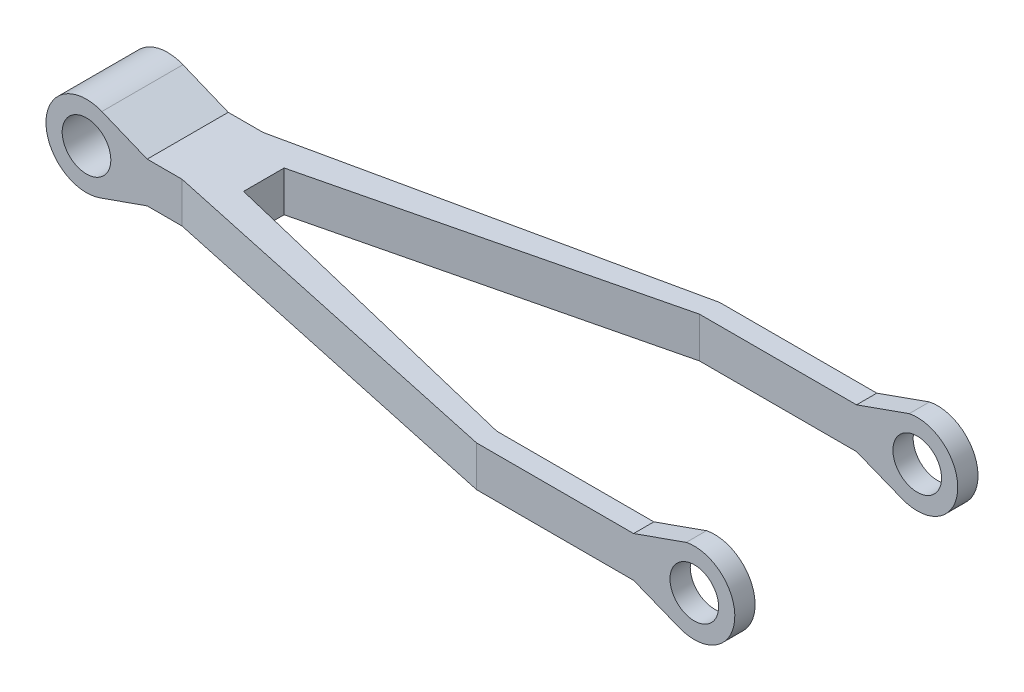
SolidWorks part; units mm, degrees
ref_plane "Front Plane" through (0, 0, 0) normal (0, 0, 1) x (1, 0, 0)
ref_plane "Top Plane" through (0, 0, 0) normal (0, 1, 0) x (1, 0, 0)
ref_plane "Right Plane" through (0, 0, 0) normal (1, 0, 0) x (0, 0, -1)
sketch "Sketch1" plane through (0, 0, 0) normal (0, 0, 1) x (1, 0, 0)
  line L0 (-349.8733, 24.6435) -> (-405.7801, 47.538)
  line L1 (350.1267, -25.3565) -> (-349.8733, -25.3565)
  line L3 (350.1267, 24.6435) -> (-349.8733, 24.6435)
  line L7 (-349.8733, -25.3565) -> (-408.1023, -45.8872)
  line L9 (0.1267, 24.6435) -> (350.1267, 24.6435) construction
  line L10 (350.1267, 24.6435) -> (415.1579, 47.7515)
  line L11 (350.1267, -25.3565) -> (406.5613, -47.7462)
  line L14 (-349.8733, 24.6435) -> (0.1267, 24.6435) construction
  arc A0 (-405.7801, 47.538) -> (-408.1023, -45.8872) centre (-424.7285, 1.2675) ccw
  arc A1 (406.5613, -47.7462) -> (401.7026, 42.9703) centre (425, -1.2703) ccw
  point P0 (0, 0)
  dimension "D4" = 100
  dimension "D5" = 100
  dimension "D1" = 700
  dimension "D2" = 50
extrude "Boss-Extrude1" add sketch "Sketch1" along normal blind 300 contours L11 A1 L10 L3 L0 A0 L7 L1
sketch "Sketch3" plane through (0, 24.6435, 0) normal (0, 1, 0) x (1, 0, 0)
  line L0 (156.3847, -275) -> (-255.9514, -175)
  line L1 (350.1267, -300) -> (-349.8733, -300) construction
  line L2 (-306.817, 0) -> (-306.817, -300) construction
  line L3 (350.1267, 0) -> (-349.8733, 0) construction
  line L4 (-306.817, -150) -> (-102.2723, -150) construction
  line L5 (-255.9514, -175) -> (-255.9514, -150)
  line L6 (-255.9514, -150) -> (-255.9514, -125)
  line L7 (-255.9514, -125) -> (156.3847, -25)
  line L8 (156.3847, -25) -> (156.3847, -150) construction
  line L9 (156.3847, -150) -> (156.3847, -275) construction
  line L10 (156.3847, -275) -> (523.2664, -275)
  line L11 (156.3847, -25) -> (646.791, -25)
  line L12 (156.3847, 0) -> (-306.817, -100)
  line L13 (156.3847, -300) -> (-306.817, -200)
  line L14 (156.3847, -300) -> (568.0939, -300)
  line L15 (568.0939, -300) -> (523.2664, -275)
  line L16 (156.3847, 0) -> (660.0038, 0)
  line L17 (660.0038, 0) -> (646.791, -25)
  line L18 (-306.817, -100) -> (-623.6055, -100)
  line L19 (-623.6055, -100) -> (-623.6055, -200)
  line L20 (-623.6055, -200) -> (-306.817, -200)
  dimension "D1" = 25
  dimension "D2" = 25
  dimension "D3" = 50
  dimension "D4" = 50
extrude "Cut-Extrude1" cut sketch "Sketch3" against normal blind 300 flip side to cut
sketch "Sketch5" plane through (0, 24.6435, 0) normal (0, 1, 0) x (1, 0, 0)
  line L0 (156.3847, -25) -> (555.9211, -25)
  line L1 (555.9211, -25) -> (555.9211, -275)
  line L2 (555.9211, -275) -> (156.3847, -275)
  line L3 (156.3847, -275) -> (-255.9514, -175) construction
  line L4 (350.1267, -275) -> (156.3847, -275) construction
  line L5 (156.3847, -25) -> (-255.9514, -125)
  line L6 (-255.9514, -125) -> (-255.9514, -175)
  line L7 (-255.9514, -175) -> (156.3847, -275)
  line L8 (-349.8733, -100) -> (-477.7336, -100)
  line L9 (-477.7336, -100) -> (-477.7336, 50.3405)
  line L10 (-477.7336, 50.3405) -> (-332.0771, 50.3405)
  line L11 (-332.0771, 50.3405) -> (-349.8733, -100)
  line L12 (-349.8733, -200) -> (-349.8733, -364.1237)
  line L13 (-349.8733, -364.1237) -> (-511.8904, -324.6474)
  line L14 (-511.8904, -324.6474) -> (-481.5194, -200)
  line L15 (-481.5194, -200) -> (-349.8733, -200)
extrude "Cut-Extrude3" cut sketch "Sketch5" along normal blind 300
sketch "Sketch6" plane through (0, 0, 200) normal (0, 0, 1) x (1, 0, 0)
  circle A0 centre (-424.7285, 1.2675) radius 30
  circle A1 centre (425, -1.2703) radius 30
  dimension "D1" = 60
extrude "Cut-Extrude4" cut sketch "Sketch6" against normal mid plane 400
sketch "Sketch7" plane through (0, 0, 300) normal (0, 0, 1) x (1, 0, 0)
  line L0 (230.9437, 251.3468) -> (230.9437, -179.9991)
  line L3 (230.9437, 251.3468) -> (540.129, 251.3468)
  line L4 (540.129, 251.3468) -> (540.129, -179.9991)
  line L5 (540.129, -179.9991) -> (230.9437, -179.9991)
sketch "Sketch8" plane through (0, 0, 300) normal (0, 0, 1) x (1, 0, 0)
  circle A0 centre (196.4644, 0) radius 15
